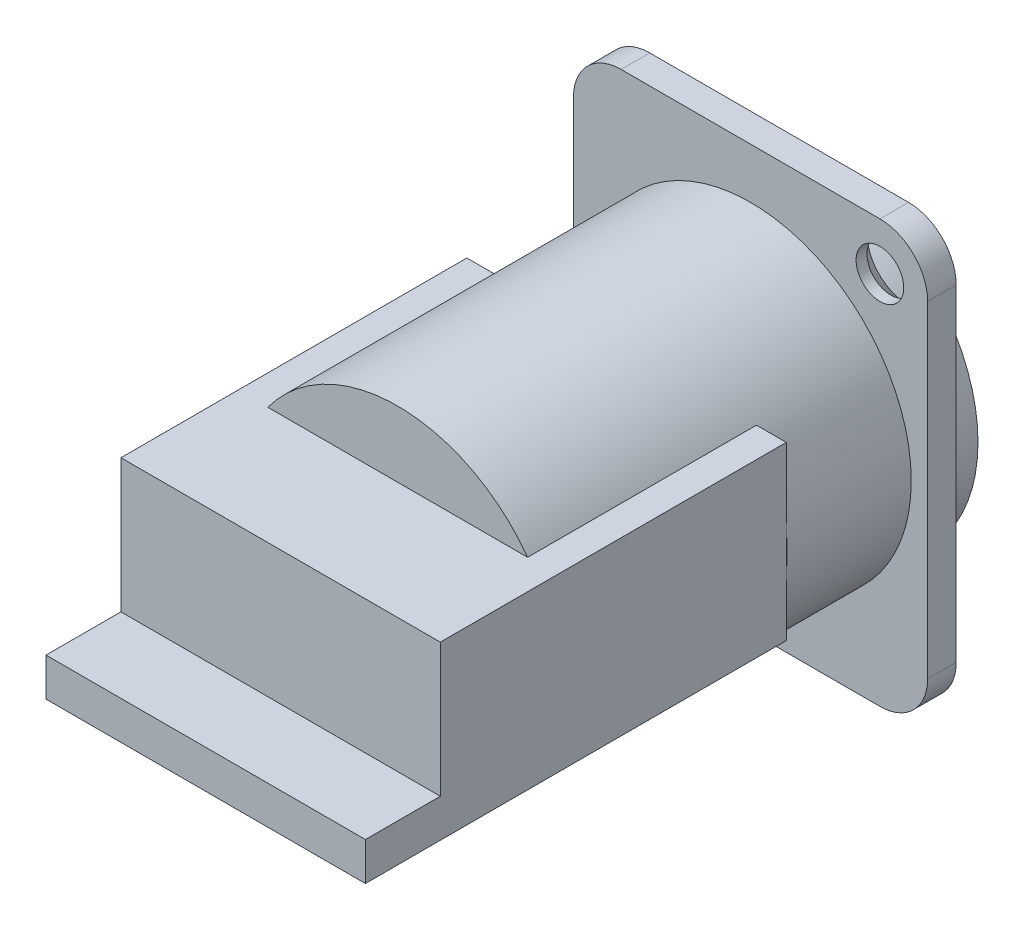
SolidWorks part; units mm, degrees
ref_plane "Plan de face" through (0, 0, 0) normal (0, 0, 1) x (1, 0, 0)
ref_plane "Plan de dessus" through (0, 0, 0) normal (0, 1, 0) x (1, 0, 0)
ref_plane "Plan de droite" through (0, 0, 0) normal (1, 0, 0) x (0, 0, -1)
ref_plane "Plan1" through (0, 0, 0) normal (0, 0, -1) x (-1, 0, 0)
sketch "Esquisse1" plane through (0, 0, 0) normal (0, 0, -1) x (-1, 0, 0)
  line L0 (13, 11.8) -> (-13, 11.8)
  line L1 (-13, 11.8) -> (-13, -15.5)
  line L2 (-13, -15.5) -> (13, -15.5)
  line L3 (13, -15.5) -> (13, 11.8)
extrude "Boss.-Extru.1" add sketch "Esquisse1" against normal blind 2.1
sketch "Esquisse2" plane through (0, 0, 2.1) normal (0, 0, 1) x (1, 0, 0)
  circle A0 centre (0, 0) radius 11.8
extrude "Boss.-Extru.2" add sketch "Esquisse2" along normal blind 40
sketch "Esquisse3" plane through (0, 11.8, 0) normal (0, 1, 0) x (-1, 0, 0)
  line L0 (-13, 2.1) -> (13, 2.1)
  line L1 (13, 2.1) -> (13, 0)
  line L2 (13, 0) -> (-13, 0)
  line L3 (-13, 0) -> (-13, 2.1)
extrude "Boss.-Extru.3" add sketch "Esquisse3" along normal blind 3.7
sketch "Esquisse4" plane through (0, 0, 0) normal (0, 0, -1) x (-1, 0, 0)
  circle A0 centre (0, 0) radius 11.8
extrude "Boss.-Extru.4" add sketch "Esquisse4" along normal blind 2.8
hole_wizard "Dégagement M181" positions "Esquisse6" profile "Esquisse5" hole size "M18" standard "Ansi Metric"
sketch "Esquisse6" plane through (0, 0, -2.8) normal (0, 0, -1) x (-1, 0, 0)
  point P0 (0, 0)
sketch "Esquisse5" plane through (0, 0, -2.8) normal (1, 0, 0) x (0, 1, 0)
  line L0 (0, 0) -> (0, 13.9)
  line L1 (0, 13.9) -> (10.45, 13.9)
  line L2 (10.45, 13.9) -> (10.45, 0)
  line L5 (10.45, 0) -> (0, 0)
  line L10 (0, 13.9) -> (-10.45, 13.9) construction
  line L11 (0, -6.35) -> (0, 107.95) construction
  dimension "Diamètre du perçage" = 20.9
  dimension "Profondeur du perçage" = 13.9
  dimension "Angle de pointe" = 180
sketch "Esquisse7" plane through (0, 0, 11.1) normal (0, 0, -1) x (-1, 0, 0)
  circle A0 centre (0, 0) radius 8.75
extrude "Boss.-Extru.5" add sketch "Esquisse7" along normal blind 10.7
sketch "Esquisse8" plane through (0, 0, 0.4) normal (0, 0, -1) x (-1, 0, 0)
  line L0 (6.35, -3.8) -> (6.35, 3.8)
  line L1 (6.35, 3.8) -> (-6.35, 3.8)
  line L2 (-6.35, 3.8) -> (-6.35, -3.8)
  line L3 (-6.35, -3.8) -> (-3.65, -3.8)
  line L4 (-3.65, -3.8) -> (-3.65, -5.6)
  line L5 (-3.65, -5.6) -> (-2.55, -5.6)
  line L6 (-2.55, -5.6) -> (-2.55, -6.9)
  line L7 (-2.55, -6.9) -> (2.55, -6.9)
  line L8 (2.55, -6.9) -> (2.55, -5.6)
  line L9 (2.55, -5.6) -> (3.65, -5.6)
  line L10 (3.65, -5.6) -> (3.65, -3.8)
  line L11 (3.65, -3.8) -> (6.35, -3.8)
extrude "Enlèv. mat.-Extru.1" cut sketch "Esquisse8" against normal blind 10.8
sketch "Esquisse9" plane through (0, 0, 11.2) normal (0, 0, -1) x (-1, 0, 0)
  line L0 (2.55, -6.9) -> (2.55, -5.65)
  line L1 (2.55, -5.65) -> (-2.55, -5.65)
  line L2 (-2.55, -5.65) -> (-2.55, -6.9)
  line L3 (-2.55, -6.9) -> (2.55, -6.9)
extrude "Enlèv. mat.-Extru.2" cut sketch "Esquisse9" against normal blind 0.5
sketch "Esquisse10" plane through (0, 0, 42.1) normal (0, 0, 1) x (1, 0, 0)
  line L0 (-11.725, -1.3283) -> (-11.725, 1.3283)
  arc A0 (-11.725, 1.3283) -> (-11.725, -1.3283) centre (0, 0) ccw
extrude "Enlèv. mat.-Extru.3" cut sketch "Esquisse10" against normal blind 30.9
ref_plane "Plan2" through (0, 0, 42.1) normal (0, 0, 1) x (1, 0, 0)
sketch "Esquisse11" plane through (0, 0, 42.1) normal (0, 0, 1) x (1, 0, 0)
  line L0 (-9.5361, 6.95) -> (-11.725, 6.95)
  line L1 (-11.725, 6.95) -> (-11.725, 1.3283)
  arc A0 (-11.725, 1.3283) -> (-9.5361, 6.95) centre (0, 0) cw
extrude "Boss.-Extru.6" add sketch "Esquisse11" against normal blind 30.9
sketch "Esquisse12" plane through (0, 0, 42.1) normal (0, 0, 1) x (1, 0, 0)
  line L0 (11.725, 1.3283) -> (11.725, -1.3283)
  arc A0 (11.725, -1.3283) -> (11.725, 1.3283) centre (0, 0) ccw
extrude "Enlèv. mat.-Extru.4" cut sketch "Esquisse12" against normal blind 30.9
sketch "Esquisse13" plane through (0, 0, 42.1) normal (0, 0, 1) x (1, 0, 0)
  line L0 (11.725, 1.3283) -> (11.725, 6.95)
  line L1 (11.725, 6.95) -> (9.5361, 6.95)
  arc A0 (9.5361, 6.95) -> (11.725, 1.3283) centre (0, 0) cw
extrude "Boss.-Extru.7" add sketch "Esquisse13" against normal blind 30.9
sketch "Esquisse14" plane through (0, 0, 42.1) normal (0, 0, 1) x (1, 0, 0)
  line L0 (-11.725, -1.3283) -> (-11.725, -5.65)
  line L1 (-11.725, -5.65) -> (-10.3594, -5.65)
  arc A0 (-10.3594, -5.65) -> (-11.725, -1.3283) centre (0, 0) cw
extrude "Boss.-Extru.8" add sketch "Esquisse14" against normal blind 30.9
sketch "Esquisse15" plane through (0, 0, 42.1) normal (0, 0, 1) x (1, 0, 0)
  line L0 (10.3594, -5.65) -> (11.725, -5.65)
  line L1 (11.725, -5.65) -> (11.725, -1.3283)
  arc A0 (11.725, -1.3283) -> (10.3594, -5.65) centre (0, 0) cw
extrude "Boss.-Extru.9" add sketch "Esquisse15" against normal blind 30.9
ref_plane "Plan3" through (0, 0, 28) normal (0, 0, -1) x (-1, 0, 0)
sketch "Esquisse17" plane through (0, 0, 28) normal (0, 0, -1) x (-1, 0, 0)
  line L0 (-9.5361, 6.95) -> (9.5361, 6.95)
  arc A0 (9.5361, 6.95) -> (-9.5361, 6.95) centre (0, 0) ccw
extrude "Enlèv. mat.-Extru.5" cut sketch "Esquisse17" against normal up to surface up to plane "Plan2"
sketch "Esquisse19" plane through (0, 0, 28) normal (0, 0, -1) x (-1, 0, 0)
  line L0 (10.3594, -5.65) -> (-10.3594, -5.65)
  arc A0 (-10.3594, -5.65) -> (10.3594, -5.65) centre (0, 0) ccw
extrude "Enlèv. mat.-Extru.6" cut sketch "Esquisse19" against normal up to surface up to plane "Plan2"
sketch "Esquisse20" plane through (-11.725, 0, 0) normal (-1, 0, 0) x (0, 0, 1)
  line L0 (42.1, 6.95) -> (36.6, 6.95)
  line L1 (36.6, 6.95) -> (36.6, -2.85)
  line L2 (36.6, -2.85) -> (42.1, -2.85)
  line L3 (42.1, -2.85) -> (42.1, 6.95)
extrude "Enlèv. mat.-Extru.7" cut sketch "Esquisse20" against normal through all
ref_plane "Plan4" through (0, -13.7792, 0) normal (0, -1, 0) x (1, 0, 0)
sketch "Esquisse21" plane through (0, -13.7792, 0) normal (0, -1, 0) x (1, 0, 0)
  line L0 (0.7, 23.6) -> (0.7, 28)
  line L1 (0.7, 28) -> (-0.7, 28)
  line L2 (-0.7, 28) -> (-0.7, 23.6)
  line L3 (-0.7, 23.6) -> (0.7, 23.6)
extrude "Boss.-Extru.10" add sketch "Esquisse21" against normal up to next
hole_wizard "Fraisage pour vis à tête fraisée M31" positions "Esquisse23" profile "Esquisse22" countersink size "M3" standard "Ansi Metric"
sketch "Esquisse23" plane through (0, 0, 0) normal (0, 0, -1) x (-1, 0, 0)
  point P0 (-9.5, 12)
  point P1 (9.5, -12)
sketch "Esquisse22" plane through (9.5, 12, 0) normal (1, 0, 0) x (0, 1, 0)
  line L0 (0, 0) -> (0, 42.1)
  line L1 (0, 42.1) -> (1.75, 42.1)
  line L2 (1.75, 42.1) -> (1.75, 1.3)
  line L3 (1.75, 1.3) -> (3.0499, 0)
  line L5 (3.0499, 0) -> (0, 0)
  line L6 (-1.75, 1.3) -> (-3.0499, 0) construction
  line L11 (0, -6.35) -> (0, 107.95) construction
  dimension "Diamètre du perçage jusqu'au prochain" = 3.5
  dimension "Profondeur du perçage jusqu'au prochain" = 42.1
  dimension "Diamètre du fraisage entrant" = 6.0999
  dimension "Angle du fraisage entrant" = 89.999
fillet "Congé1" radius 3.5 4 edges at (-13, 15.5, 1.05) (13, 15.5, 1.05) (-13, -15.5, 1.05) (13, -15.5, 1.05)
